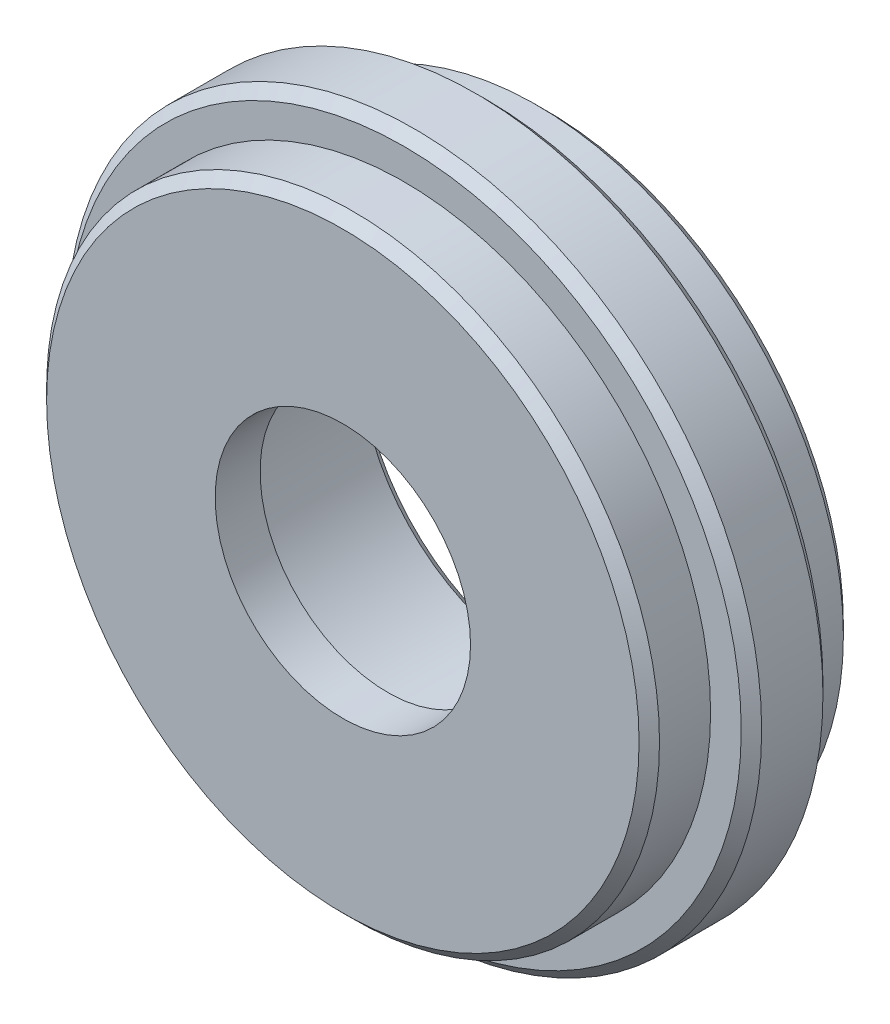
SolidWorks part; units mm, degrees
ref_plane "Front" through (0, 0, 0) normal (0, 0, 1) x (1, 0, 0)
ref_plane "Top" through (0, 0, 0) normal (0, 1, 0) x (1, 0, 0)
ref_plane "Right" through (0, 0, 0) normal (1, 0, 0) x (0, 0, -1)
sketch "Sketch1" plane through (0, 0, 0) normal (0, 0, 1) x (1, 0, 0)
  circle A0 centre (0, 0) radius 19.05
  circle A1 centre (0, 0) radius 10.9873
  dimension "D1" = 38.1
  dimension "D2" = 21.9746
extrude "Boss-Extrude1" add sketch "Sketch1" along normal mid plane 12.7
sketch "Sketch2" plane through (0, 0, 0) normal (0, 0, 1) x (1, 0, 0)
  circle A0 centre (0, 0) radius 21.59
  circle A1 centre (0, 0) radius 19.05 construction
  circle A2 centre (0, 0) radius 10.9873 construction
  circle A3 centre (0, 0) radius 10.9873
  dimension "D1" = 2.54
extrude "Boss-Extrude2" add sketch "Sketch2" along normal mid plane 5.08
sketch "Sketch3" plane through (0, 0, 6.35) normal (0, 0, 1) x (1, 0, 0)
  circle A0 centre (0, 0) radius 10.9873
  circle A1 centre (0, 0) radius 10.9873 construction
  circle A2 centre (0, 0) radius 7.9375
  dimension "D1" = 15.875
extrude "Boss-Extrude3" add sketch "Sketch3" against normal blind 2.794
chamfer "Chamfer1" distance 0.635 angle 45 4 edges at (19.05, 0, -6.35) (19.05, 0, 6.35) (21.59, 0, -2.54) (21.59, 0, 2.54)
chamfer "Chamfer2" distance 0.635 angle 45 1 edges at (10.9873, 0, -6.35)
